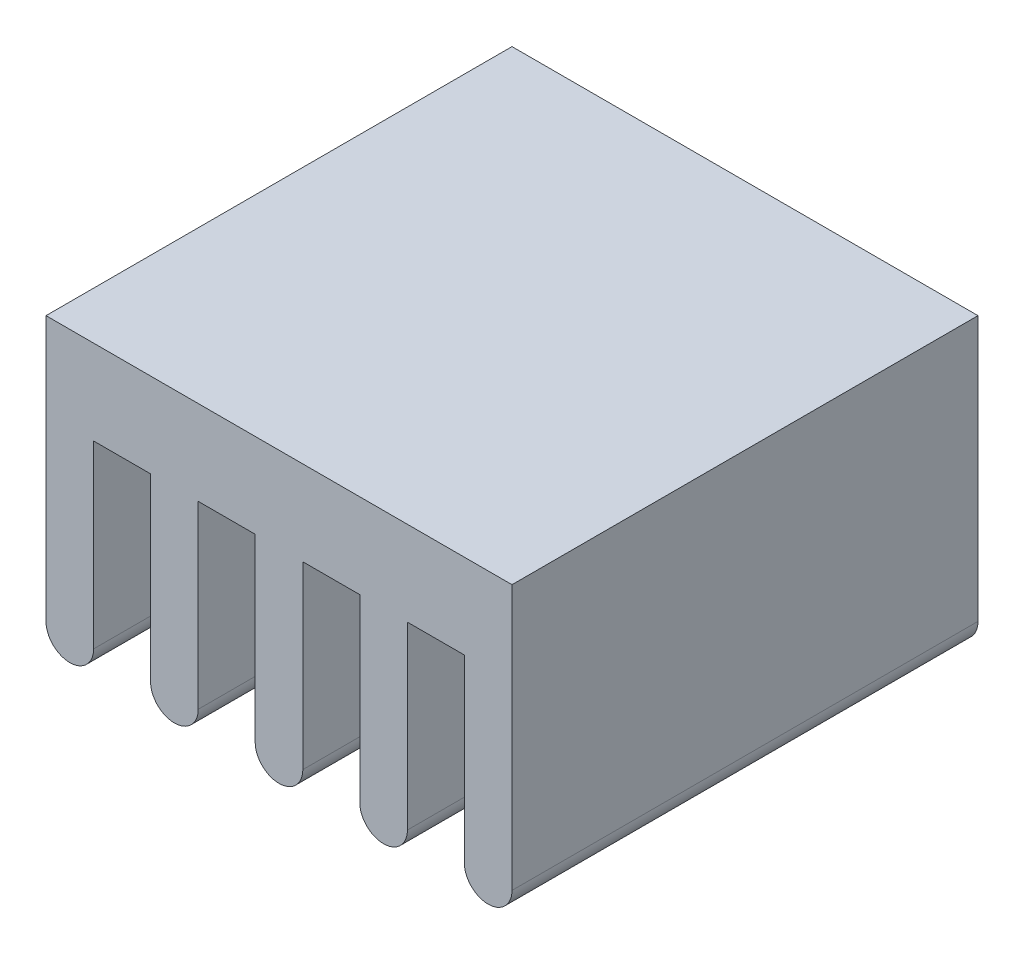
SolidWorks part; units mm, degrees
ref_plane "Plano frontal" through (0, 0, 0) normal (0, 0, 1) x (1, 0, 0)
ref_plane "Plano superior" through (0, 0, 0) normal (0, 1, 0) x (1, 0, 0)
ref_plane "Plano direito" through (0, 0, 0) normal (1, 0, 0) x (0, 0, -1)
sketch "Esboço1" plane through (0, 0, 0) normal (0, 0, 1) x (1, 0, 0)
  line L0 (0, 0) -> (8.8, 0)
  line L1 (8.8, 0) -> (8.8, -5)
  line L3 (0, 0) -> (0, -5)
  line L4 (0.9, -1.6) -> (1.975, -1.6)
  line L5 (0.9, -1.6) -> (0.9, -5)
  line L6 (1.975, -1.6) -> (1.975, -5)
  line L8 (2.875, -5) -> (2.875, -1.6)
  line L9 (2.875, -1.6) -> (3.95, -1.6)
  line L10 (3.95, -1.6) -> (3.95, -5)
  line L12 (4.85, -5) -> (4.85, -1.6)
  line L13 (4.85, -1.6) -> (5.925, -1.6)
  line L14 (5.925, -1.6) -> (5.925, -5)
  line L16 (6.825, -5) -> (6.825, -1.6)
  line L17 (6.825, -1.6) -> (7.9, -1.6)
  line L18 (7.9, -1.6) -> (7.9, -5)
  arc A0 (0, -5) -> (0.9, -5) centre (0.45, -5) ccw
  arc A1 (1.975, -5) -> (2.875, -5) centre (2.425, -5) ccw
  arc A2 (3.95, -5) -> (4.85, -5) centre (4.4, -5) ccw
  arc A3 (5.925, -5) -> (6.825, -5) centre (6.375, -5) ccw
  arc A4 (7.9, -5) -> (8.8, -5) centre (8.35, -5) ccw
  dimension "D2" = 5
  dimension "D13" = 0.45
  dimension "D3" = 1.6
  dimension "D4" = 0.9
  dimension "D5" = 0.9
  dimension "D6" = 1.075
  dimension "D7" = 0.9
  dimension "D8" = 1.075
  dimension "D9" = 0.9
  dimension "D10" = 1.075
  dimension "D11" = 0.9
  dimension "D12" = 1.075
extrude "Ressalto-extrusão1" add sketch "Esboço1" along normal mid plane 8.8
